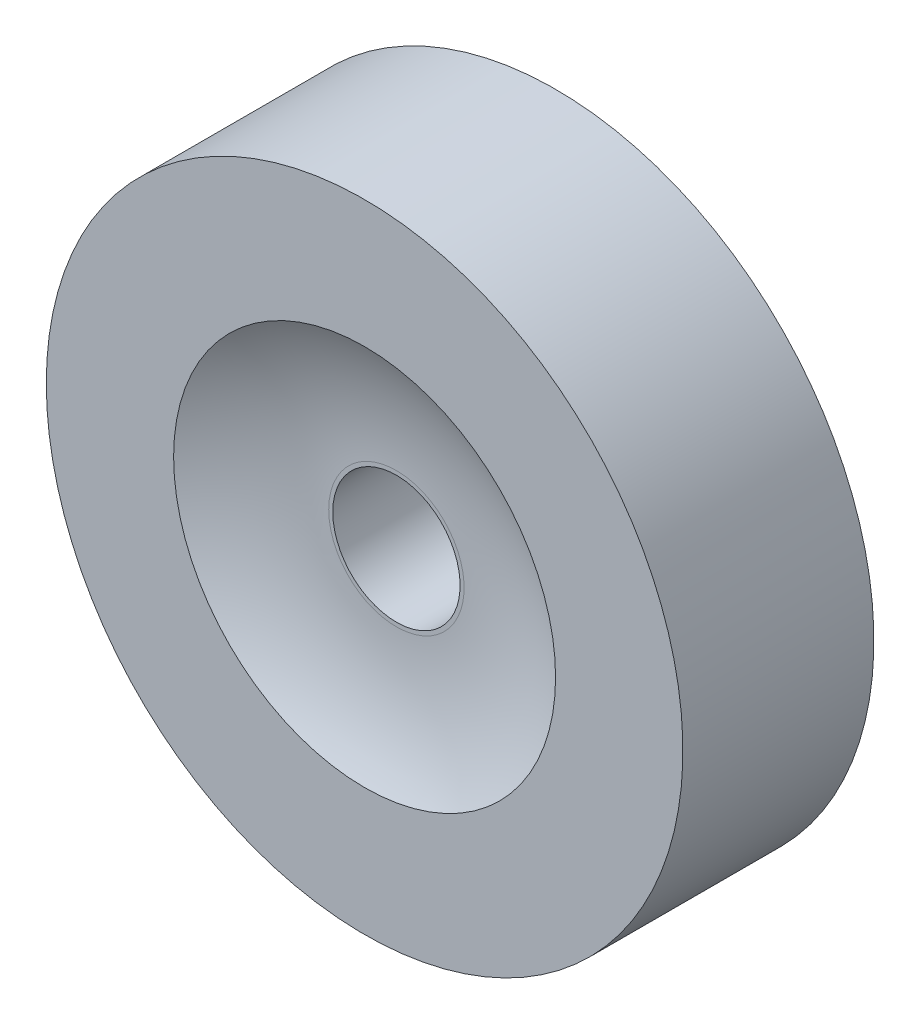
SolidWorks part; units mm, degrees
ref_plane "Alzado" through (0, 0, 0) normal (0, 0, 1) x (1, 0, 0)
ref_plane "Planta" through (0, 0, 0) normal (0, 1, 0) x (1, 0, 0)
ref_plane "Vista lateral" through (0, 0, 0) normal (1, 0, 0) x (0, 0, -1)
ref_plane "Plane1" through (0, -7.8054, 0) normal (0, -1, 0) x (1, 0, 0)
sketch "Sketch1" plane through (0, -7.8054, 0) normal (0, -1, 0) x (1, 0, 0)
  line L0 (7.5844, 0.2) -> (7.5844, 0.5)
  line L1 (7.5844, 0.5) -> (7.3844, 0.5)
  line L2 (7.1907, 0.45) -> (7.1844, 0.45)
  line L3 (7.1844, 0.45) -> (7.1844, 0.2)
  line L4 (7.1844, 0.2) -> (7.5844, 0.2)
  line L5 (7.0844, 0.5) -> (7.0844, 0.2) construction
  arc A0 (7.3844, 0.5) -> (7.1907, 0.45) centre (7.1907, 0.85) cw
  dimension "D1" = 0.4
  dimension "D2" = 0.1
  dimension "D3" = 0.1064
  dimension "D4" = 0.3
  dimension "D5" = 0.5
  dimension "D6" = 0.25
revolve "Revolve1" add sketch "Sketch1" angle 360 about L5
